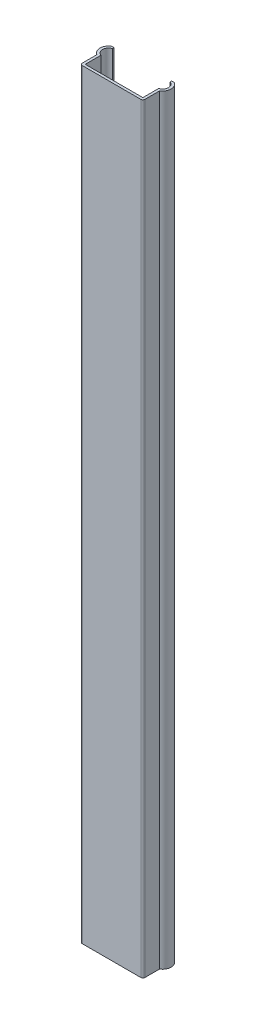
SolidWorks part; units mm, degrees
ref_plane "Face" through (0, 0, 0) normal (0, 0, 1) x (1, 0, 0)
ref_plane "Dessus" through (0, 0, 0) normal (0, 1, 0) x (1, 0, 0)
ref_plane "Droite" through (0, 0, 0) normal (1, 0, 0) x (0, 0, -1)
sketch "Esquisse1" plane through (0, 0, 0) normal (0, 1, 0) x (1, 0, 0)
  line L0 (7.5, 0) -> (-7.5, 0)
  line L1 (-7.5, 0) -> (-7.5, 4)
  line L2 (0, 0) -> (0, 28.714) construction
  line L3 (6.9, 0.6) -> (-6.9, 0.6)
  line L4 (-6.9, 0.6) -> (-6.9, 4.3853)
  line L5 (-7.5, 4) -> (-7.5, 7.5) construction
  line L6 (-6.9, 4.3853) -> (-6.9, 7.5) construction
  line L7 (-6.9, 7.5) -> (-6.9, 7.1147)
  line L8 (-7.5, 7.5) -> (-6.9, 7.5)
  line L9 (-8.5, 0) -> (-8.5, 8.9289) construction
  line L10 (6.9, 7.5) -> (6.9, 7.1147)
  line L11 (7.5, 7.5) -> (6.9, 7.5)
  line L12 (6.9, 0.6) -> (6.9, 4.3853)
  line L13 (7.5, 0) -> (7.5, 4)
  arc A0 (-7.5, 4) -> (-7.5, 7.5) centre (-6.4688, 5.75) cw
  arc A1 (-6.9, 4.3853) -> (-6.9, 7.1147) centre (-6.4688, 5.75) cw
  arc A2 (6.9, 4.3853) -> (6.9, 7.1147) centre (6.4688, 5.75) ccw
  arc A3 (7.5, 4) -> (7.5, 7.5) centre (6.4688, 5.75) ccw
  point P22 (0, 0.6)
  dimension "D6" = 0.6
  dimension "D1" = 0.6
  dimension "D2" = 0.6
  dimension "D3" = 7.5
  dimension "D4" = 4
  dimension "D5" = 7.5
  dimension "D7" = 8.5
extrude "Extrusion1" add sketch "Esquisse1" along normal blind 182
fillet "Congé1" radius 0.5 2 edges at (-7.5, 91, 0) (7.5, 91, 0)
